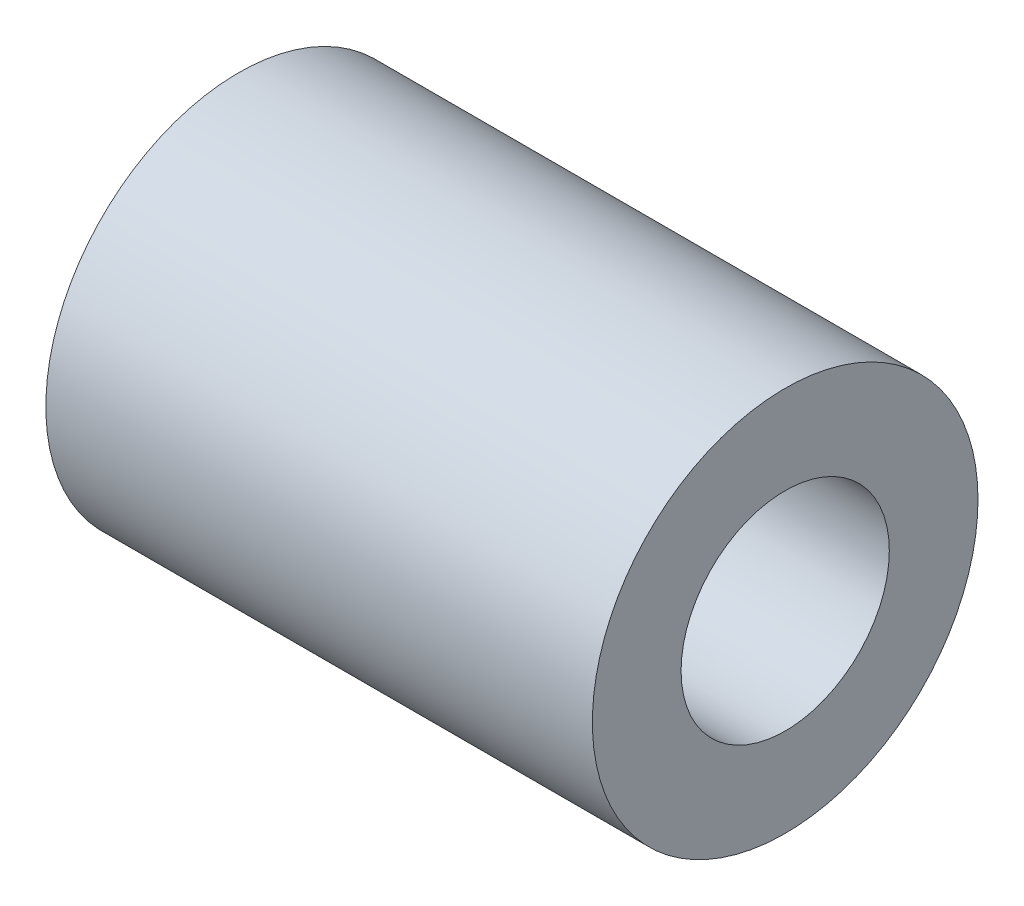
SolidWorks part; units mm, degrees
ref_plane "Plan de face" through (0, 0, 0) normal (0, 0, 1) x (1, 0, 0)
ref_plane "Plan de dessus" through (0, 0, 0) normal (0, 1, 0) x (1, 0, 0)
ref_plane "Plan de droite" through (0, 0, 0) normal (1, 0, 0) x (0, 0, -1)
sketch "Esquisse1" plane through (0, 0, 0) normal (1, 0, 0) x (0, 0, -1)
  circle A0 centre (0, 0) radius 3.429
  circle A1 centre (0, 0) radius 6.35
  dimension "D1" = 6.858
  dimension "D2" = 12.7
extrude "Boss.-Extru.1" add sketch "Esquisse1" against normal blind 18
equation "\"D1@Boss.-Extru.1\"=18mm"
